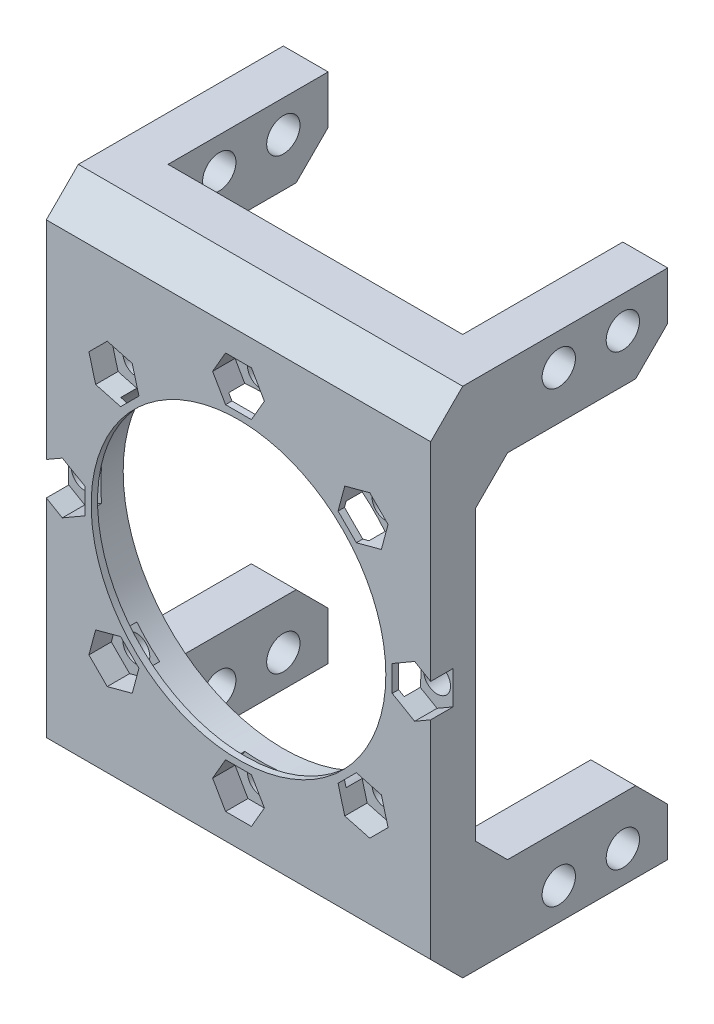
SolidWorks part; units mm, degrees
ref_plane "Front Plane" through (0, 0, 0) normal (0, 0, 1) x (1, 0, 0)
ref_plane "Top Plane" through (0, 0, 0) normal (0, 1, 0) x (1, 0, 0)
ref_plane "Right Plane" through (0, 0, 0) normal (1, 0, 0) x (0, 0, -1)
sketch "Sketch1" plane through (0, 0, 0) normal (0, 0, 1) x (1, 0, 0)
  line L1 (0, 0) -> (60, 0)
  line L2 (0, 0) -> (0, 80)
  line L3 (0, 80) -> (60, 80)
  line L4 (60, 0) -> (60, 80)
  dimension "D1" = 60
  dimension "D2" = 80
extrude "Boss-Extrude1" add sketch "Sketch1" along normal blind 7
sketch "Sketch2" plane through (0, 0, 0) normal (0, 0, -1) x (-1, 0, 0)
  line L1 (0, 80) -> (-7, 80)
  line L2 (0, 80) -> (0, 67.5)
  line L3 (0, 67.5) -> (-7, 67.5)
  line L4 (-7, 80) -> (-7, 67.5)
  dimension "D1" = 7
  dimension "D2" = 12.5
extrude "Boss-Extrude2" add sketch "Sketch2" along normal blind 30
sketch "Sketch3" plane through (0, 0, 0) normal (-1, 0, 0) x (0, 0, 1)
  line L0 (7, 80) -> (7, 0) construction
  line L1 (7, 80) -> (-30, 80) construction
  circle A0 centre (-13, 75) radius 2.6
  circle A1 centre (-23, 75) radius 2.6
  dimension "D1" = 20
  dimension "D2" = 5.2
  dimension "D3" = 5
  dimension "D4" = 5.2
  dimension "D5" = 10
extrude "Cut-Extrude1" cut sketch "Sketch3" against normal blind 50
sketch "Sketch4" plane through (0, 0, 7) normal (0, 0, 1) x (1, 0, 0)
  circle A0 centre (30, 40) radius 25
  dimension "D1" = 50
extrude "Cut-Extrude2" cut sketch "Sketch4" against normal through all
sketch "Sketch6" plane through (0, 0, 7) normal (0, 0, 1) x (1, 0, 0)
  circle A0 centre (30, 67.5) radius 2.1
  circle A2 centre (49.4454, 59.4454) radius 2.1
  circle A3 centre (57.5, 40) radius 2.1
  circle A4 centre (49.4454, 20.5546) radius 2.1
  circle A5 centre (30, 12.5) radius 2.1
  circle A6 centre (10.5546, 20.5546) radius 2.1
  circle A7 centre (2.5, 40) radius 2.1
  circle A8 centre (10.5546, 59.4454) radius 2.1
  point P21 (30, 40)
  dimension "D2" = 4.2
  dimension "D3" = 8
extrude "Cut-Extrude3" cut sketch "Sketch6" against normal through all
sketch "Sketch7" plane through (0, 0, 0) normal (-1, 0, 0) x (0, 0, 1)
  line L0 (7, 40) -> (2.4678, 40) construction
  line L1 (7, 80) -> (7, 0) construction
ref_plane "Plane1" through (0, 40, 0) normal (0, -1, 0) x (0, 0, -1)
mirror "Mirror1" about plane through (0, 40, 0) normal (0, -1, 0) of "Cut-Extrude1", "Boss-Extrude2"
sketch "Sketch8" plane through (0, 80, 0) normal (0, 1, 0) x (1, 0, 0)
  line L0 (30, -7) -> (30, -1.1613) construction
  line L1 (60, -7) -> (0, -7) construction
ref_plane "Plane2" through (30, 0, 0) normal (1, 0, 0) x (0, 0, -1)
mirror "Mirror2" about plane through (30, 0, 0) normal (1, 0, 0) of "Mirror1", "Cut-Extrude1", "Boss-Extrude2"
chamfer "Chamfer1" distance 5 angle 45 4 edges at (56.5, 12.5, 0) (3.5, 12.5, 0) (3.5, 67.5, 0) (56.5, 67.5, 0)
chamfer "Chamfer2" distance 5 angle 45 4 edges at (3.5, 67.5, -30) (56.5, 67.5, -30) (56.5, 12.5, -30) (3.5, 12.5, -30)
sketch "Sketch9" plane through (0, 0, 0) normal (0, 0, -1) x (-1, 0, 0)
  line L1 (-53, 80) -> (-7, 80)
  line L2 (-53, 80) -> (-53, 72.5)
  line L3 (-53, 72.5) -> (-7, 72.5)
  line L4 (-7, 80) -> (-7, 72.5)
  line L5 (-53, 7.5) -> (-7, 7.5)
  line L6 (-53, 7.5) -> (-53, 0)
  line L7 (-53, 0) -> (-7, 0)
  line L8 (-7, 7.5) -> (-7, 0)
extrude "Boss-Extrude4" add sketch "Sketch9" along normal blind 5
chamfer "Chamfer3" distance 5 angle 45 2 edges at (30, 0, 7) (30, 80, 7)
sketch "Sketch20" plane through (0, 0, 7) normal (0, 0, 1) x (1, 0, 0)
  circle A0 centre (30, 40) radius 25
  circle A1 centre (30, 40) radius 23
  dimension "D1" = 46
extrude "Boss-Extrude5" add sketch "Sketch20" against normal blind 1
sketch "Sketch21" plane through (0, 0, 7) normal (0, 0, 1) x (1, 0, 0)
  line L0 (52.3032, 56.5877) -> (53.3492, 60.4914)
  line L1 (34.0415, 67.5) -> (32.0207, 71)
  line L2 (32.0207, 71) -> (27.9793, 71)
  line L3 (27.9793, 71) -> (25.9585, 67.5)
  line L4 (25.9585, 67.5) -> (27.9793, 64)
  line L5 (27.9793, 64) -> (32.0207, 64)
  line L6 (32.0207, 64) -> (34.0415, 67.5)
  line L7 (53.3492, 60.4914) -> (50.4914, 63.3492)
  line L8 (50.4914, 63.3492) -> (46.5877, 62.3032)
  line L9 (46.5877, 62.3032) -> (45.5417, 58.3994)
  line L10 (45.5417, 58.3994) -> (48.3994, 55.5417)
  line L11 (48.3994, 55.5417) -> (52.3032, 56.5877)
  line L12 (57.5, 35.9585) -> (61, 37.9793)
  line L13 (61, 37.9793) -> (61, 42.0207)
  line L14 (61, 42.0207) -> (57.5, 44.0415)
  line L15 (57.5, 44.0415) -> (54, 42.0207)
  line L16 (54, 42.0207) -> (54, 37.9793)
  line L17 (54, 37.9793) -> (57.5, 35.9585)
  line L18 (46.5877, 17.6968) -> (50.4914, 16.6508)
  line L19 (50.4914, 16.6508) -> (53.3492, 19.5086)
  line L20 (53.3492, 19.5086) -> (52.3032, 23.4123)
  line L21 (52.3032, 23.4123) -> (48.3994, 24.4583)
  line L22 (48.3994, 24.4583) -> (45.5417, 21.6006)
  line L23 (45.5417, 21.6006) -> (46.5877, 17.6968)
  line L24 (25.9585, 12.5) -> (27.9793, 9)
  line L25 (27.9793, 9) -> (32.0207, 9)
  line L26 (32.0207, 9) -> (34.0415, 12.5)
  line L27 (34.0415, 12.5) -> (32.0207, 16)
  line L28 (32.0207, 16) -> (27.9793, 16)
  line L29 (27.9793, 16) -> (25.9585, 12.5)
  line L30 (7.6968, 23.4123) -> (6.6508, 19.5086)
  line L31 (6.6508, 19.5086) -> (9.5086, 16.6508)
  line L32 (9.5086, 16.6508) -> (13.4123, 17.6968)
  line L33 (13.4123, 17.6968) -> (14.4583, 21.6006)
  line L34 (14.4583, 21.6006) -> (11.6006, 24.4583)
  line L35 (11.6006, 24.4583) -> (7.6968, 23.4123)
  line L36 (2.5, 44.0415) -> (-1, 42.0207)
  line L37 (-1, 42.0207) -> (-1, 37.9793)
  line L38 (-1, 37.9793) -> (2.5, 35.9585)
  line L39 (2.5, 35.9585) -> (6, 37.9793)
  line L40 (6, 37.9793) -> (6, 42.0207)
  line L41 (6, 42.0207) -> (2.5, 44.0415)
  line L42 (13.4123, 62.3032) -> (9.5086, 63.3492)
  line L43 (9.5086, 63.3492) -> (6.6508, 60.4914)
  line L44 (6.6508, 60.4914) -> (7.6968, 56.5877)
  line L45 (7.6968, 56.5877) -> (11.6006, 55.5417)
  line L46 (11.6006, 55.5417) -> (14.4583, 58.3994)
  line L47 (14.4583, 58.3994) -> (13.4123, 62.3032)
  circle A0 centre (30, 67.5) radius 3.5 construction
  point P53 (30, 40)
  dimension "D1" = 7
  dimension "D2" = 8
extrude "Cut-Extrude5" cut sketch "Sketch21" against normal blind 3.5
